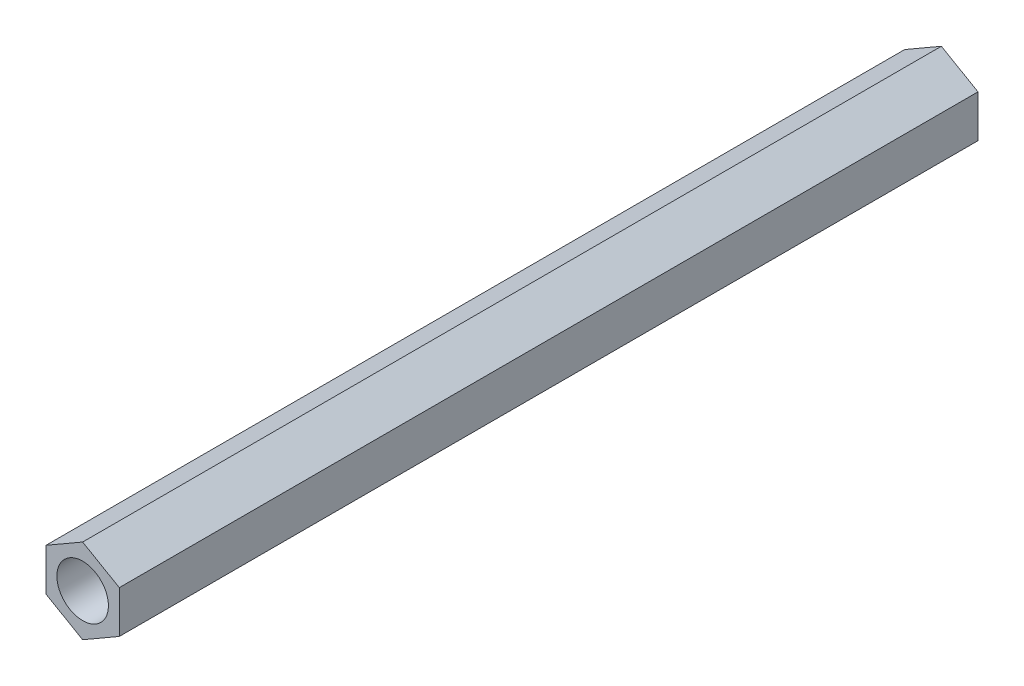
SolidWorks part; units mm, degrees
ref_plane "前视基准面" through (0, 0, 0) normal (0, 0, 1) x (1, 0, 0)
ref_plane "上视基准面" through (0, 0, 0) normal (0, 1, 0) x (1, 0, 0)
ref_plane "右视基准面" through (0, 0, 0) normal (1, 0, 0) x (0, 0, -1)
sketch "草图1" plane through (0, 0, 0) normal (0, 0, 1) x (1, 0, 0)
  line L1 (0, 2.4639) -> (-2.1338, 1.232)
  line L2 (-2.1338, 1.232) -> (-2.1338, -1.232)
  line L3 (-2.1338, -1.232) -> (0, -2.4639)
  line L4 (0, -2.4639) -> (2.1338, -1.232)
  line L5 (2.1338, -1.232) -> (2.1338, 1.232)
  line L6 (2.1338, 1.232) -> (0, 2.4639)
  circle A0 centre (0, 0) radius 1.5
  circle A1 centre (0, 0) radius 2.1338 construction
extrude "凸台-拉伸1" add sketch "草图1" along normal blind 50
